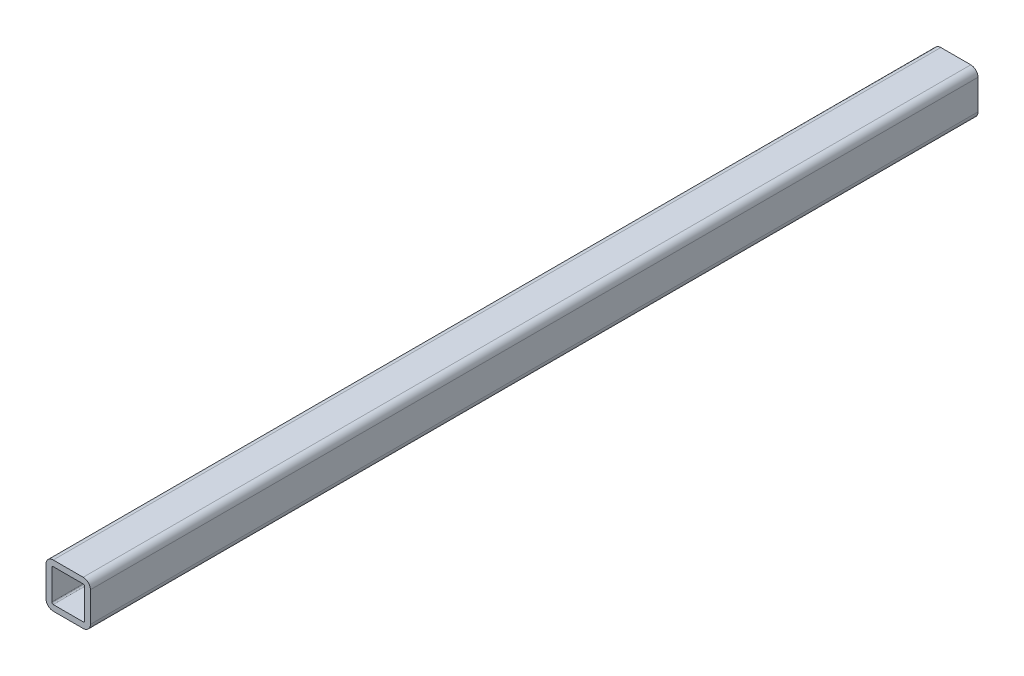
SolidWorks part; units mm, degrees
material "AISI 304"
ref_plane "Front" through (0, 0, 0) normal (0, 0, 1) x (1, 0, 0)
ref_plane "Top" through (0, 0, 0) normal (0, 1, 0) x (1, 0, 0)
ref_plane "Right" through (0, 0, 0) normal (1, 0, 0) x (0, 0, -1)
sketch "Sketch1" plane through (0, 0, 0) normal (0, 0, 1) x (1, 0, 0)
  line L0 (-4.699, 0) -> (-6.35, 0) construction
  line L1 (4.2863, -6.35) -> (-4.2863, -6.35)
  line L2 (6.35, -4.2863) -> (6.35, 4.2863)
  line L3 (4.2863, 6.35) -> (-4.2863, 6.35)
  line L4 (-6.35, -4.2863) -> (-6.35, 4.2863)
  line L5 (6.35, -6.35) -> (-6.35, 6.35) construction
  line L6 (6.35, 6.35) -> (-6.35, -6.35) construction
  line L7 (4.2863, 4.699) -> (-4.2863, 4.699)
  line L8 (4.699, 4.2863) -> (4.699, -4.2863)
  line L9 (4.2863, -4.699) -> (-4.2863, -4.699)
  line L10 (-4.699, 4.2863) -> (-4.699, -4.2863)
  line L11 (4.699, 4.699) -> (-4.699, -4.699) construction
  line L12 (4.699, -4.699) -> (-4.699, 4.699) construction
  line L13 (0, -4.699) -> (0, -6.35) construction
  arc A0 (-4.2863, -4.699) -> (-4.699, -4.2863) centre (-4.2863, -4.2863) cw
  arc A1 (4.699, -4.2863) -> (4.2863, -4.699) centre (4.2863, -4.2863) cw
  arc A2 (4.2863, 4.699) -> (4.699, 4.2863) centre (4.2863, 4.2863) cw
  arc A3 (-4.2863, 4.699) -> (-4.699, 4.2863) centre (-4.2863, 4.2863) ccw
  arc A4 (4.2863, -6.35) -> (6.35, -4.2863) centre (4.2863, -4.2863) ccw
  arc A5 (6.35, 4.2863) -> (4.2863, 6.35) centre (4.2863, 4.2863) ccw
  arc A6 (-4.2863, 6.35) -> (-6.35, 4.2863) centre (-4.2863, 4.2863) ccw
  arc A7 (-4.2863, -6.35) -> (-6.35, -4.2863) centre (-4.2863, -4.2863) cw
  point P0 (0, 0)
  point P6 (0, 0)
  dimension "D4" = 2.0638
  dimension "Outside Width" = 12.7
  dimension "Ouside Height" = 12.7
  dimension "D5" = 1.651
  dimension "Inside Width" = 9.398
  dimension "Wall Thickness" = 1.651
sketch "Sketch2" plane through (0, 0, 0) normal (1, 0, 0) x (0, 0, -1)
  line L0 (-127, 0) -> (127, 0) construction
  line L1 (127, -6.35) -> (127, 6.35)
  line L2 (-127, -6.35) -> (-127, 6.35)
  line L3 (0, -6.35) -> (0, 6.35) construction
  point P3 (-115.8875, 0)
  point P6 (127, 0)
  point P9 (-127, 0)
  point P12 (0, 0)
  point P13 (115.8875, 0)
  dimension "D1" = 11.1125
  dimension "Length" = 254
sketch "Sketch4" plane through (0, 0, 0) normal (0, 0, 1) x (1, 0, 0)
  line L0 (6.35, -4.2863) -> (6.35, 4.2863) construction
  line L1 (4.2863, 6.35) -> (-4.2863, 6.35) construction
  line L2 (-6.35, -4.2863) -> (-6.35, 4.2863) construction
  line L3 (4.2863, -6.35) -> (-4.2863, -6.35) construction
  line L4 (4.699, 4.2863) -> (4.699, -4.2863) construction
  line L5 (4.2863, -4.699) -> (-4.2863, -4.699) construction
  line L6 (-4.699, 4.2863) -> (-4.699, -4.2863) construction
  line L7 (4.2863, 4.699) -> (-4.2863, 4.699) construction
  line L8 (6.35, -4.2863) -> (6.35, 4.2863)
  line L9 (4.2863, 6.35) -> (-4.2863, 6.35)
  line L10 (-6.35, -4.2863) -> (-6.35, 4.2863)
  line L11 (4.2863, -6.35) -> (-4.2863, -6.35)
  line L12 (4.699, 4.2863) -> (4.699, -4.2863)
  line L13 (4.2863, -4.699) -> (-4.2863, -4.699)
  line L14 (-4.699, 4.2863) -> (-4.699, -4.2863)
  line L15 (4.2863, 4.699) -> (-4.2863, 4.699)
  arc A0 (6.35, 4.2863) -> (4.2863, 6.35) centre (4.2863, 4.2863) ccw construction
  arc A1 (-4.2863, 6.35) -> (-6.35, 4.2863) centre (-4.2863, 4.2863) ccw construction
  arc A2 (-6.35, -4.2863) -> (-4.2863, -6.35) centre (-4.2863, -4.2863) ccw construction
  arc A3 (4.2863, -6.35) -> (6.35, -4.2863) centre (4.2863, -4.2863) ccw construction
  arc A4 (4.2863, -4.699) -> (4.699, -4.2863) centre (4.2863, -4.2863) ccw construction
  arc A5 (-4.699, -4.2863) -> (-4.2863, -4.699) centre (-4.2863, -4.2863) ccw construction
  arc A6 (-4.2863, 4.699) -> (-4.699, 4.2863) centre (-4.2863, 4.2863) ccw construction
  arc A7 (4.699, 4.2863) -> (4.2863, 4.699) centre (4.2863, 4.2863) ccw construction
  arc A8 (6.35, 4.2863) -> (4.2863, 6.35) centre (4.2863, 4.2863) ccw
  arc A9 (-4.2863, 6.35) -> (-6.35, 4.2863) centre (-4.2863, 4.2863) ccw
  arc A10 (-6.35, -4.2863) -> (-4.2863, -6.35) centre (-4.2863, -4.2863) ccw
  arc A11 (4.2863, -6.35) -> (6.35, -4.2863) centre (4.2863, -4.2863) ccw
  arc A12 (4.2863, -4.699) -> (4.699, -4.2863) centre (4.2863, -4.2863) ccw
  arc A13 (-4.699, -4.2863) -> (-4.2863, -4.699) centre (-4.2863, -4.2863) ccw
  arc A14 (-4.2863, 4.699) -> (-4.699, 4.2863) centre (-4.2863, 4.2863) ccw
  arc A15 (4.699, 4.2863) -> (4.2863, 4.699) centre (4.2863, 4.2863) ccw
extrude "Boss-Extrude1" add sketch "Sketch4" along normal mid plane 254
equation "\"D1@Sketch2\"=\"Outside Width@Sketch1\"*.875"
equation "\"D1@Boss-Extrude1\"=\"Length@Sketch2\""
equation "\"D4@Sketch1\"=\"D5@Sketch1\"*1.25"
